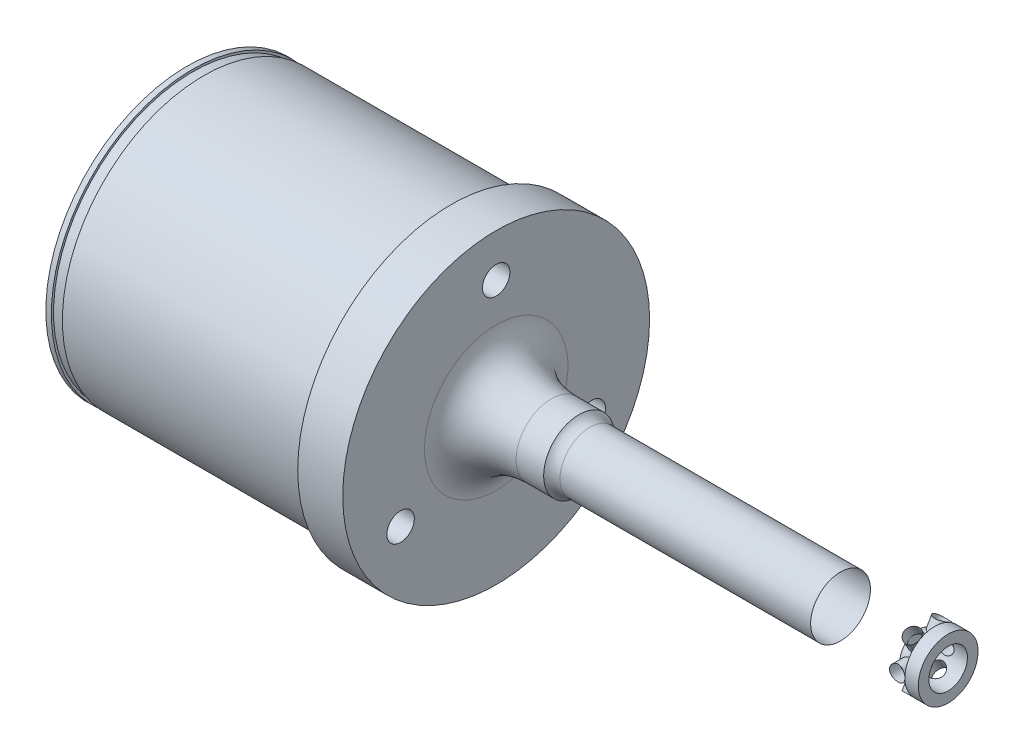
SolidWorks part; units mm, degrees
material "AISI 4340 Steel, normalized"
ref_plane "Front Plane" through (0, 0, 0) normal (0, 0, 1) x (1, 0, 0)
ref_plane "Top Plane" through (0, 0, 0) normal (0, 1, 0) x (1, 0, 0)
ref_plane "Right Plane" through (0, 0, 0) normal (1, 0, 0) x (0, 0, -1)
sketch "Sketch1" plane through (0, 0, 0) normal (0, 0, 1) x (1, 0, 0)
  line L0 (-132.526, 0) -> (143.2472, 0) construction
  line L1 (0, 16.51) -> (0, 35.306)
  line L2 (0, 35.306) -> (-10.3632, 35.306)
  line L3 (-10.3632, 35.306) -> (-10.3632, 32.766)
  line L4 (-10.3632, 32.766) -> (-71.12, 32.766)
  line L5 (-71.12, 32.766) -> (-71.12, 0)
  line L6 (-71.12, 0) -> (104.013, 0)
  line L7 (104.013, 0) -> (104.013, 6.8834)
  line L8 (104.013, 6.8834) -> (21.5708, 6.8834)
  line L9 (19.05, 8.128) -> (12.7, 8.128)
  arc A0 (21.5708, 6.8834) -> (19.05, 8.128) centre (21.5708, 10.0584) cw
  ellipse E0 centre (12.7, 16.51) end of major axis (25.4, 16.51) minor radius 8.382 (0, 16.51) -> (12.7, 8.128) ccw
  dimension "D9" = 3.175
  dimension "D1" = 13.7668
  dimension "D2" = 10.3632
  dimension "D3" = 65.532
  dimension "D4" = 70.612
  dimension "D5" = 16.256
  dimension "D6" = 104.013
  dimension "D7" = 71.12
  dimension "D8" = 33.02
  dimension "D10" = 12.7
  dimension "D11" = 6.35
revolve "Base Revolve" add sketch "Sketch1" angle 360 about L0
ref_axis "Centerline" through (116.6455, 0, 0) along (-1, 0, 0)
ref_plane "Thread Start" through (100.9396, 0, 0) normal (1, 0, 0) x (0, 0, -1)
ref_plane "Thread End" through (79.248, 0, 0) normal (1, 0, 0) x (0, 0, -1)
split line "Thread Split End"
split line "Thread Split Start"
sketch "Sketch4" plane through (0, 0, 0) normal (1, 0, 0) x (0, 0, -1)
  line L0 (0, 25.4) -> (0, 0) construction
  circle A0 centre (0, 25.4) radius 3.1623
  dimension "D1" = 6.3246
  dimension "D2" = 25.4
extrude "Dowel Pin Hole" cut sketch "Sketch4" against normal through all
pattern_circular "CirPattern1" count 3 over 360 about axis through (0, 0, 0) along (1, 0, 0) of "Dowel Pin Hole"
sketch "Sketch9" plane through (0, 0, 0) normal (0, 0, 1) x (1, 0, 0)
  line L0 (100.9396, 6.8834) -> (100.9396, -6.8834) construction
  line L1 (100.9396, 6.8834) -> (100.9396, -6.8834) construction
  line L2 (116.6455, 0) -> (-95.9774, 0) construction
  circle A0 centre (99.1616, 0) radius 1.778
  dimension "D1" = 3.556
extrude "Cotter Pin Hole" cut sketch "Sketch9" against normal mid plane 55.88
pattern_circular "CirPattern3" count 3 over 360 about axis through (116.6455, 0, 0) along (-1, 0, 0) of "Cotter Pin Hole"
sketch "Sketch10" plane through (104.013, 0, 0) normal (1, 0, 0) x (0, 0, -1)
  circle A0 centre (0, 0) radius 4.445
  circle A1 centre (0, 0) radius 6.8834 construction
  dimension "D1" = 8.89
extrude "Shank Tip Relief" cut sketch "Sketch10" against normal blind 6.731
sketch "Sketch5" plane through (-71.12, 0, 0) normal (-1, 0, 0) x (0, 0, 1)
  line L0 (0, 0) -> (0, 19.5326) construction
  line L1 (-0.5588, 19.5326) -> (0.5588, 19.5326) construction
  line L2 (0, 19.5326) -> (-12.827, 19.5326) construction
  line L3 (-1.27, -24.3763) -> (1.27, -24.3763) construction
  arc A0 (-11.6404, 14.0226) -> (11.6404, 14.0226) centre (0, 0) ccw
  arc A1 (10.0194, 27.7351) -> (-10.0194, 27.7351) centre (0, 0) ccw
  arc A2 (-11.6404, 14.0226) -> (-10.0194, 27.7351) centre (0.5588, 19.5326) cw
  arc A3 (11.6404, 14.0226) -> (10.0194, 27.7351) centre (-0.5588, 19.5326) ccw
  arc A4 (10.0194, 27.7351) -> (-10.0194, 27.7351) centre (0, 0) cw construction
  arc A5 (-1.0057, -19.3032) -> (-1.5343, -29.4495) centre (-1.27, -24.3763) ccw
  arc A6 (1.5343, -29.4495) -> (1.0057, -19.3032) centre (1.27, -24.3763) ccw
  arc A7 (-1.5343, -29.4495) -> (1.5343, -29.4495) centre (0, 0) ccw
  arc A8 (-1.0057, -19.3032) -> (1.0057, -19.3032) centre (0, 0) ccw
  dimension "D1" = 36.449
  dimension "D2" = 19.5326
  dimension "D3" = 13.3858
  dimension "D4" = 29.4894
  dimension "D7" = 10.16
  dimension "D5" = 12.827
  dimension "D6" = 2.54
extrude "Tulip Pattern" cut sketch "Sketch5" against normal offset from surface (66.04 mm away) 5.08 up to face at (0, -9.9614, 23.5782)
pattern_circular "CirPattern2" count 3 over 360 about axis through (0, 0, 0) along (1, 0, 0) of "Tulip Pattern"
fillet "Fillet1" radius 6.985 6 edges at (-38.1, -5.1905, -29.029) (-38.1, -22.5446, -19.0096) (-38.1, -22.5446, 19.0096) (-38.1, -5.1905, 29.029) (-38.1, 27.7351, 10.0194) (-38.1, 27.7351, -10.0194)
sketch "Sketch8" plane through (-71.12, 0, 0) normal (-1, 0, 0) x (0, 0, 1)
  circle A1 centre (0, 0) radius 30.607
  dimension "D1" = 61.214
extrude "Tulip Depth" cut sketch "Sketch8" against normal offset from surface (20.32 mm away) 45.72 up to face at (-5.08, 0, 0)
sketch "Sketch7" plane through (0, 0, 0) normal (0, 0, 1) x (1, 0, 0)
  line L0 (-5.08, 29.4894) -> (-5.08, 28.5623)
  line L1 (-5.08, 22.2377) -> (-5.08, -18.2245)
  line L2 (-5.08, 13.2859) -> (-5.08, 0)
  line L3 (-5.08, 0) -> (-2.032, 0)
  line L4 (-5.08, 0) -> (-32.512, 0) construction
  line L5 (-6.1758, 15.3439) -> (-72.3886, -23.2328) construction
  line L6 (-46.0849, 23.2965) -> (-41.6991, 15.7687) construction
  line L7 (-52.0185, 9.7565) -> (-31.3797, 21.781) construction
  line L9 (-41.6991, 15.7687) -> (-32.512, 0) construction
  line L11 (-50.8, 30.607) -> (-50.8, -30.607) construction
  line L12 (-60.7418, -27.4709) -> (-74.4455, -35.4548) construction
  line L13 (-56.4043, 17.2842) -> (-35.7655, 29.3087) construction
  line L14 (-60.7418, -27.4709) -> (-70.3318, -11.0108) construction
  line L15 (-74.4455, -35.4548) -> (-84.0354, -18.9947) construction
  line L16 (-0.8862, 19.5326) -> (-50.8, 19.5326) construction
  line L17 (-54.8764, 13.1329) -> (-32.9076, 25.9323) construction
  line L18 (-70.3318, -11.0108) -> (-84.0354, -18.9947) construction
  line L19 (-60.7418, -27.4709) -> (-84.0354, -18.9947) construction
  line L20 (-74.4455, -35.4548) -> (-70.3318, -11.0108) construction
  arc A1 (-2.032, 0) -> (-5.08, 13.2859) centre (-32.512, 0) ccw
  arc A2 (-56.4043, 17.2842) -> (-52.0185, 9.7565) centre (-43.892, 19.5326) ccw construction
  arc A3 (-35.7655, 29.3087) -> (-31.3797, 21.781) centre (-43.892, 19.5326) cw construction
  point P24 (-72.3886, -23.2328)
  dimension "D1" = 30.48
  dimension "D2" = 3.048
  dimension "D3" = 25.4254
  dimension "D4" = 8.7122
  dimension "D5" = 19.05
  dimension "D6" = 19.5326
revolve "Axle Relief" cut sketch "Sketch7" angle 360 about L4
sketch "Sketch11" plane through (0, 0, 0) normal (0, 0, 1) x (1, 0, 0)
  line L0 (-10.3632, -35.306) -> (-10.3632, -32.766)
  line L1 (-10.3632, 32.766) -> (-10.3632, 35.306)
  line L2 (-10.3632, 34.3829) -> (-10.3632, 35.306)
  line L3 (-10.3632, -35.306) -> (-10.3632, -32.766)
  line L4 (-10.922, 32.5183) -> (-67.31, 32.5183)
  line L6 (-82.412, 0) -> (108.1661, 0) construction
  line L7 (116.6455, 0) -> (-95.9774, 0) construction
  line L8 (-10.3632, 35.306) -> (0, 35.306)
  line L9 (0, -35.306) -> (-10.3632, -35.306)
  line L11 (-10.3632, 35.306) -> (0, 35.306) construction
  line L12 (-10.3632, 32.766) -> (-10.3632, 32.6858) construction
  line L14 (-10.3632, 35.306) -> (-10.3632, -35.306) construction
  line L15 (-71.12, -32.766) -> (-71.12, -30.607)
  line L16 (-71.12, 30.607) -> (-71.12, 32.766)
  line L17 (-71.12, 35.306) -> (-71.12, 32.5183)
  line L18 (-71.12, 32.766) -> (-71.12, -32.766) construction
  line L19 (-71.12, 32.5183) -> (-69.85, 32.5183)
  line L20 (-69.85, 32.5183) -> (-69.85, 32.0104)
  line L21 (-69.85, 32.0104) -> (-67.31, 32.0104)
  line L22 (-67.31, 32.5183) -> (-67.31, 32.0104)
  line L23 (-71.12, 35.306) -> (-10.3632, 35.306)
  arc A0 (-10.922, 32.5183) -> (-10.3632, 34.3829) centre (-10.922, 33.5344) ccw
  dimension "D1" = 1.016
  dimension "D2" = 0.5588
  dimension "D3" = 65.0367
  dimension "D4" = 0.0802
  dimension "D5" = 1.27
  dimension "D6" = 2.54
  dimension "D7" = 0.508
revolve "Final Cut" cut sketch "Sketch11" angle 360 about axis through (116.6455, 0, 0) along (-1, 0, 0)
